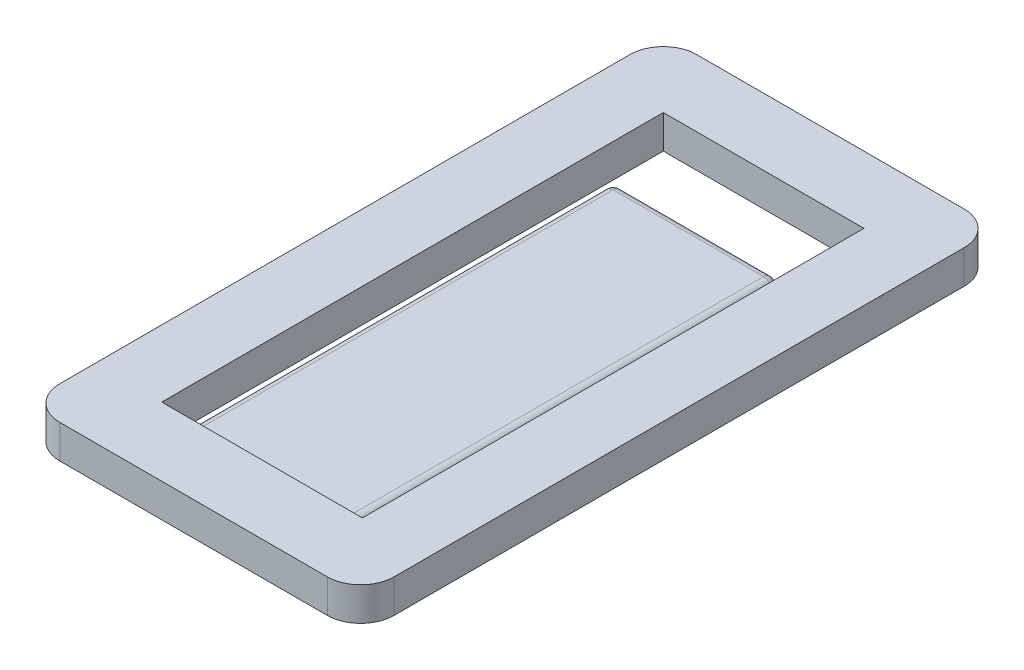
SolidWorks part; units mm, degrees
ref_plane "Front Plane" through (0, 0, 0) normal (0, 0, 1) x (1, 0, 0)
ref_plane "Top Plane" through (0, 0, 0) normal (0, 1, 0) x (1, 0, 0)
ref_plane "Right Plane" through (0, 0, 0) normal (1, 0, 0) x (0, 0, -1)
sketch "Sketch1" plane through (0, 0, 0) normal (0, 1, 0) x (1, 0, 0)
  line L1 (-5, 9.525) -> (5, 9.525)
  line L2 (-5, 9.525) -> (-5, -9.525)
  line L3 (-5, -9.525) -> (5, -9.525)
  line L4 (5, 9.525) -> (5, -9.525)
  line L5 (-5, 9.525) -> (5, -9.525) construction
  line L6 (-5, -9.525) -> (5, 9.525) construction
  point P0 (0, 0)
  dimension "D1" = 10
  dimension "D2" = 19.05
extrude "Boss-Extrude1" add sketch "Sketch1" along normal blind 1
sketch "Sketch2" plane through (0, 1, 0) normal (0, 1, 0) x (1, 0, 0)
  line L0 (-5, 9.525) -> (-5, -9.525) construction
  line L1 (-3, -7.475) -> (-2.5, -7.475)
  line L2 (-3, -7.475) -> (-3, 7.525)
  line L3 (-3, 7.525) -> (-2.5, 7.525)
  line L4 (-2.5, -7.475) -> (-2.5, 7.525)
  line L5 (5, 9.525) -> (-5, 9.525) construction
  dimension "D1" = 2
  dimension "D2" = 0.5
  dimension "D3" = 15
  dimension "D4" = 2
extrude "Cut-Extrude1" cut sketch "Sketch2" against normal through all and the other way through all
sketch "Sketch3" plane through (0, 1, 0) normal (0, 1, 0) x (1, 0, 0)
  line L0 (5, -9.525) -> (5, 9.525) construction
  line L1 (2.5, -7.475) -> (3, -7.475)
  line L2 (2.5, -7.475) -> (2.5, 7.525)
  line L3 (2.5, 7.525) -> (3, 7.525)
  line L4 (3, -7.475) -> (3, 7.525)
  line L5 (5, 9.525) -> (-5, 9.525) construction
  dimension "D1" = 15
  dimension "D2" = 2
  dimension "D3" = 0.5
  dimension "D4" = 2
extrude "Cut-Extrude2" cut sketch "Sketch3" against normal through all
sketch "Sketch4" plane through (0, 1, 0) normal (0, 1, 0) x (1, 0, 0)
  line L0 (2.5, 7.525) -> (2.5, -7.475) construction
  line L1 (-2.5, 7.525) -> (2.5, 7.525)
  line L2 (-2.5, 7.525) -> (-2.5, 5.525)
  line L3 (-2.5, 5.525) -> (2.5, 5.525)
  line L4 (2.5, 7.525) -> (2.5, 5.525)
  dimension "D1" = 2
extrude "Cut-Extrude3" cut sketch "Sketch4" against normal through all
sketch "Sketch5" plane through (0, 1, 0) normal (0, 1, 0) x (1, 0, 0)
  line L1 (-2.5, 5.525) -> (2.5, 5.525)
  line L2 (-2.5, 5.525) -> (-2.5, -7.475)
  line L3 (-2.5, -7.475) -> (2.5, -7.475)
  line L4 (2.5, 5.525) -> (2.5, -7.475)
extrude "Cut-Extrude4" cut sketch "Sketch5" against normal blind 0.5
fillet "Fillet9" radius 0.25 1 edges at (0, 0.5, -5.525)
fillet "Fillet10" radius 0.25 3 edges at (-2.5, 0.125, -5.525) (-2.5, 0.5, 1.1) (-2.5, 0.4268, -5.4518)
fillet "Fillet11" radius 0.25 3 edges at (2.5, 0.125, -5.525) (2.5, 0.5, 1.1) (2.5, 0.4268, -5.4518)
fillet "Fillet13" radius 1 1 edges at (-5, 0.5, -9.525)
fillet "Fillet14" radius 1 1 edges at (5, 0.5, -9.525)
fillet "Fillet15" radius 1 1 edges at (5, 0.5, 9.525)
fillet "Fillet16" radius 1 1 edges at (-5, 0.5, 9.525)
